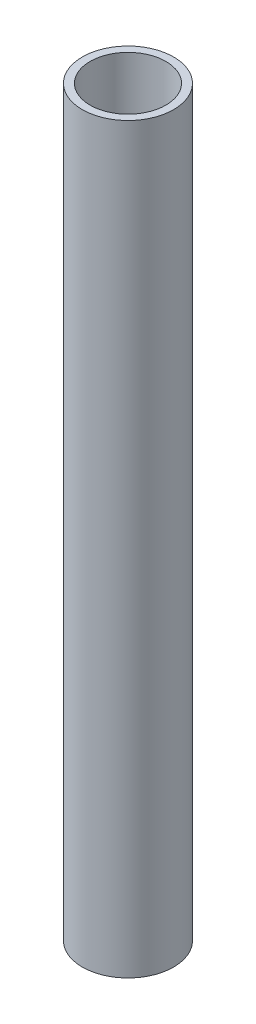
SolidWorks part; units mm, degrees
material "6061 Alloy"
ref_plane "Front Plane" through (0, 0, 0) normal (0, 0, 1) x (1, 0, 0)
ref_plane "Top Plane" through (0, 0, 0) normal (0, 1, 0) x (1, 0, 0)
ref_plane "Right Plane" through (0, 0, 0) normal (1, 0, 0) x (0, 0, -1)
sketch "Sketch1" plane through (0, 0, 0) normal (0, 1, 0) x (1, 0, 0)
  circle A0 centre (0, 0) radius 21.082
  circle A1 centre (0, 0) radius 17.5006
  dimension "D1" = 42.164
  dimension "D2" = 35.0012
extrude "Boss-Extrude1" add sketch "Sketch1" along normal blind 342.9
